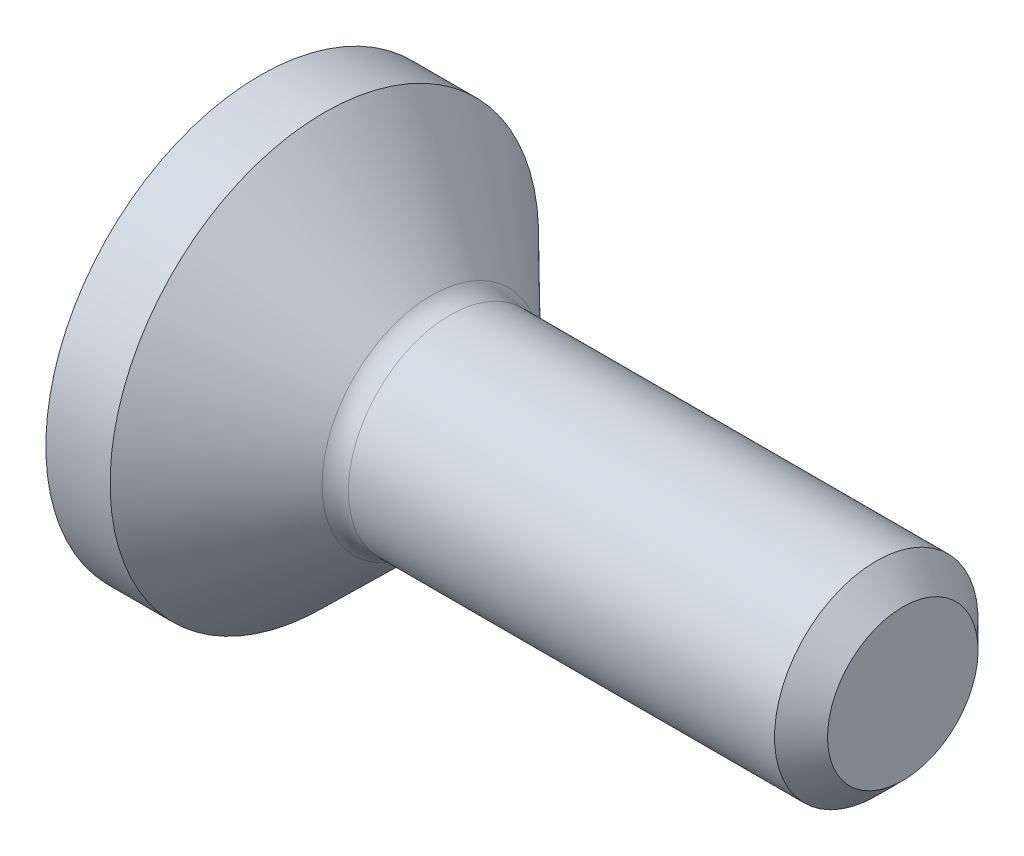
SolidWorks part; units mm, degrees
ref_plane "Front" through (0, 0, 0) normal (0, 0, 1) x (1, 0, 0)
ref_plane "Top" through (0, 0, 0) normal (0, 1, 0) x (1, 0, 0)
ref_plane "Right" through (0, 0, 0) normal (1, 0, 0) x (0, 0, -1)
sketch "Sketch1" plane through (0, 0, 0) normal (0, 0, 1) x (1, 0, 0)
  line L0 (1.7749, 0.95) -> (5.7525, 0.95)
  line L1 (5.7525, 0.95) -> (6, 0.7025)
  line L2 (6, 0.7025) -> (6, 0)
  line L3 (1.6, 1.0213) -> (0.6, 2)
  line L4 (0.6, 2) -> (0, 2)
  line L5 (0, 2) -> (0, 0)
  line L6 (0, 0) -> (6, 0)
  line L7 (0, 0) -> (-0.9177, 0) construction
  arc A0 (1.7749, 0.95) -> (1.6, 1.0213) centre (1.7749, 1.2) cw
  dimension "D1" = 6
  dimension "D4" = 0.25
  dimension "D2" = 4
  dimension "D3" = 0.6
  dimension "D5" = 1.9
  dimension "D6" = 135
  dimension "D7" = 0.35
  dimension "D8" = 1.6
revolve "Revolve1" add sketch "Sketch1" angle 360 about L7
sketch "Sketch2" plane through (0, 0, 0) normal (-1, 0, 0) x (0, 0, 1)
  line L1 (0.75, 0.433) -> (0, 0.866)
  line L2 (0, 0.866) -> (-0.75, 0.433)
  line L3 (-0.75, 0.433) -> (-0.75, -0.433)
  line L4 (-0.75, -0.433) -> (0, -0.866)
  line L5 (0, -0.866) -> (0.75, -0.433)
  line L6 (0.75, -0.433) -> (0.75, 0.433)
  circle A0 centre (0, 0) radius 0.75 construction
  dimension "D1" = 1.5
extrude "Cut-Extrude1" cut sketch "Sketch2" against normal blind 1.5
